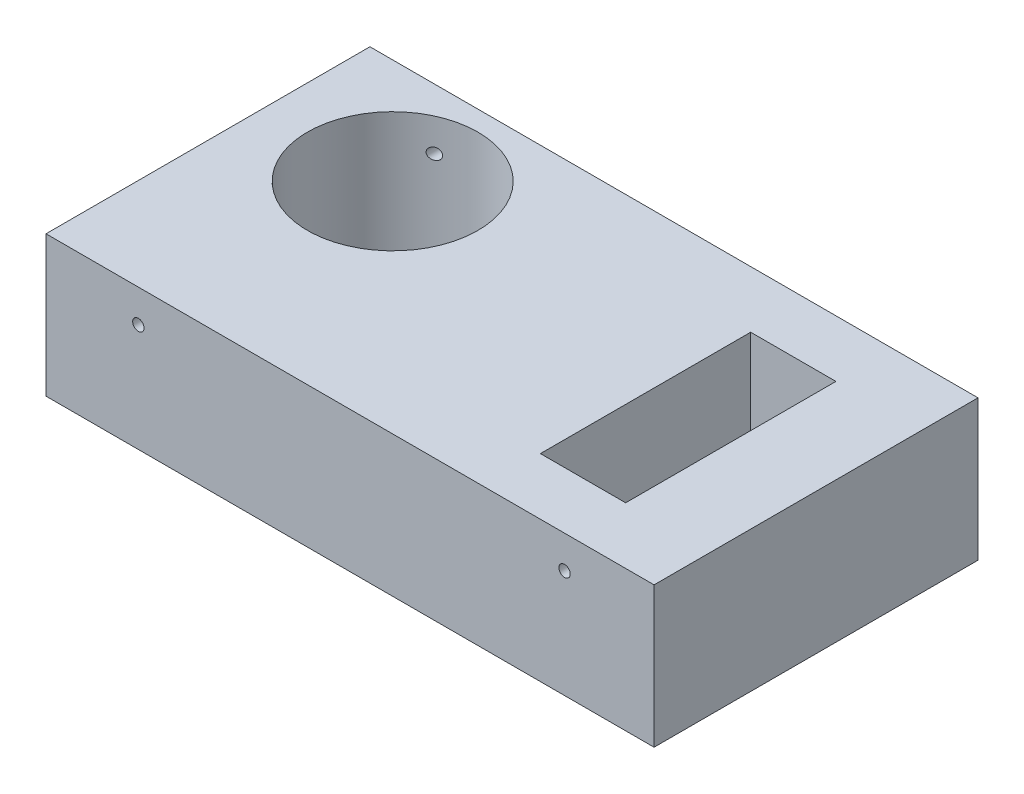
SolidWorks part; units mm, degrees
ref_plane "Front Plane" through (0, 0, 0) normal (0, 0, 1) x (1, 0, 0)
ref_plane "Top Plane" through (0, 0, 0) normal (0, 1, 0) x (1, 0, 0)
ref_plane "Right Plane" through (0, 0, 0) normal (1, 0, 0) x (0, 0, -1)
sketch "Sketch1" plane through (0, 0, 0) normal (0, 1, 0) x (1, 0, 0)
  line L1 (107, 57) -> (-107, 57)
  line L2 (107, 57) -> (107, -57)
  line L3 (107, -57) -> (-107, -57)
  line L4 (-107, 57) -> (-107, -57)
  line L5 (107, 57) -> (-107, -57) construction
  line L6 (107, -57) -> (-107, 57) construction
  point P0 (0, 0)
  dimension "D1" = 214
  dimension "D2" = 114
extrude "Boss-Extrude1" add sketch "Sketch1" along normal blind 49.5
sketch "Sketch2" plane through (0, 0, 57) normal (0, 0, 1) x (1, 0, 0)
  line L0 (-107, 49.5) -> (-107, 0) construction
  line L1 (-107, 0) -> (107, 0) construction
  circle A0 centre (-74.5, 38) radius 2
  circle A1 centre (75.5, 38) radius 2
  point P6 (0, 0)
  dimension "D1" = 32.5
  dimension "D2" = 150
  dimension "D3" = 38
  dimension "D4" = 4
extrude "Cut-Extrude1" cut sketch "Sketch2" against normal through all
sketch "Sketch4" plane through (0, 0, 0) normal (0, -1, 0) x (1, 0, 0)
  line L0 (-107, -57) -> (-107, 57) construction
  line L1 (107, -57) -> (-107, -57) construction
  line L2 (107, 57) -> (107, -57) construction
  line L3 (77, 37) -> (47, 37)
  line L4 (77, 37) -> (77, -37)
  line L5 (77, -37) -> (47, -37)
  line L6 (47, 37) -> (47, -37)
  line L7 (-107, 57) -> (107, 57) construction
  circle A0 centre (-62, -20) radius 30
  dimension "D1" = 60
  dimension "D2" = 45
  dimension "D3" = 37
  dimension "D4" = 30
  dimension "D5" = 30
  dimension "D6" = 20
  dimension "D7" = 20
extrude "Cut-Extrude2" cut sketch "Sketch4" against normal blind 55
